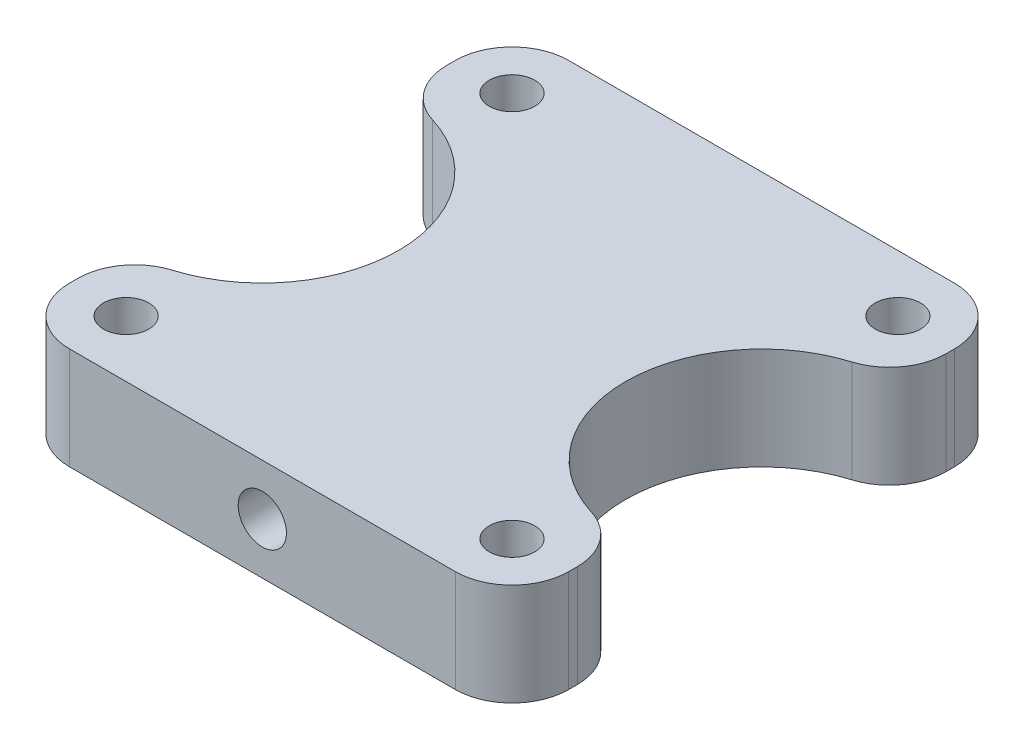
SolidWorks part; units mm, degrees
ref_plane "Front Plane" through (0, 0, 0) normal (0, 0, 1) x (1, 0, 0)
ref_plane "Top Plane" through (0, 0, 0) normal (0, 1, 0) x (1, 0, 0)
ref_plane "Right Plane" through (0, 0, 0) normal (1, 0, 0) x (0, 0, -1)
sketch "Sketch1" plane through (0, 0, 0) normal (0, 1, 0) x (1, 0, 0)
  line L1 (-44, -44) -> (44, -44)
  line L2 (-44, -44) -> (-44, 44)
  line L3 (-44, 44) -> (44, 44)
  line L4 (44, -44) -> (44, 44)
  line L5 (-44, -44) -> (44, 44) construction
  line L6 (-44, 44) -> (44, -44) construction
  point P0 (0, 0)
  dimension "D1" = 88
extrude "Boss-Extrude1" add sketch "Sketch1" along normal blind 18 contours L2 L1 L4 L3
fillet "Fillet1" radius 10 4 edges at (-44, 9, -44) (44, 9, -44) (44, 9, 44) (-44, 9, 44)
sketch "Sketch2" plane through (0, 18, 0) normal (0, 1, 0) x (1, 0, 0)
  circle A0 centre (-34, 34) radius 2.15
  circle A1 centre (34, 34) radius 2.15
  circle A2 centre (34, -34) radius 2.15
  circle A3 centre (-34, -34) radius 2.15
  dimension "D1" = 4.3
extrude "Cut-Extrude1" cut sketch "Sketch2" against normal through all
sketch "Sketch5" plane through (0, 18, 0) normal (0, 1, 0) x (1, 0, 0)
  circle A0 centre (-34, 34) radius 4
  circle A1 centre (34, 34) radius 4
  circle A2 centre (34, -34) radius 4
  circle A3 centre (-34, -34) radius 4
  dimension "D1" = 8
extrude "Cut-Extrude4" cut sketch "Sketch5" against normal offset from surface (13 mm away) 5 up to face at (-34, 0, 36.15)
sketch "Sketch6" plane through (0, 0, 44) normal (0, 0, 1) x (1, 0, 0)
  line L0 (-1034, 9) -> (48966, 9) construction
  line L1 (-34, 18) -> (-34, 0) construction
  circle A0 centre (0, 9) radius 4.25
  point P4 (0, 0)
  point P8 (-34, 9)
  point P10 (0, 0)
  dimension "D1" = 8.5
extrude "Cut-Extrude5" cut sketch "Sketch6" against normal blind 40
chamfer "Chamfer1" distance 20 angle 1 1 edges at (4.25, 9, 4)
sketch "Sketch7" plane through (0, 18, 0) normal (0, 1, 0) x (1, 0, 0)
  line L0 (-44, -34) -> (-44, 34) construction
  line L1 (44, -34) -> (44, 34) construction
  line L2 (-20, -1000) -> (-20, 49000) construction
  line L3 (20, -1000) -> (20, 49000) construction
  circle A0 centre (-44, 0) radius 24
  circle A1 centre (44, 0) radius 24
  dimension "D1" = 40
extrude "Cut-Extrude6" cut sketch "Sketch7" against normal through all
fillet "Fillet2" radius 10 4 edges at (44, 9, -24) (44, 9, 24) (-44, 9, 24) (-44, 9, -24)
